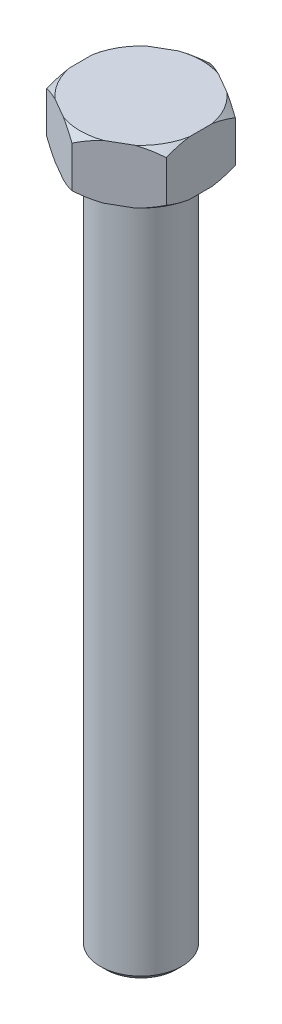
SolidWorks part; units mm, degrees
ref_plane "Front Plane" through (0, 0, 0) normal (0, 0, 1) x (1, 0, 0)
ref_plane "Top Plane" through (0, 0, 0) normal (0, 1, 0) x (1, 0, 0)
ref_plane "Right Plane" through (0, 0, 0) normal (1, 0, 0) x (0, 0, -1)
sketch "Sketch1" plane through (0, 0, 0) normal (0, 1, 0) x (1, 0, 0)
  line L1 (-11, 6.3509) -> (-11, -6.3509)
  line L2 (-11, -6.3509) -> (0, -12.7017)
  line L3 (0, -12.7017) -> (11, -6.3509)
  line L4 (11, -6.3509) -> (11, 6.3509)
  line L5 (11, 6.3509) -> (0, 12.7017)
  line L6 (0, 12.7017) -> (-11, 6.3509)
  circle A0 centre (0, 0) radius 11 construction
  point P1 (0, 0)
  point P10 (0, 0)
  dimension "D1" = 22
extrude "Boss-Extrude1" add sketch "Sketch1" along normal blind 10 contours L1 L2 L3 L4 L5 L6
sketch "Sketch2" plane through (0, 0, 0) normal (0, -1, 0) x (1, 0, 0)
  circle A0 centre (0, 0) radius 7.5
  dimension "D1" = 15
extrude "Boss-Extrude2" add sketch "Sketch2" along normal blind 126
cosmetic thread "Cosmetic Thread1"
chamfer "Chamfer1" distance 1 angle 45 1 edges at (0, -126, -7.5)
sketch "Sketch4" plane through (0, 0, 0) normal (1, 0, 0) x (0, 0, -1)
  line L0 (0, 0) -> (0, 22.1948) construction
  line L1 (12.7017, 10) -> (12.7017, 8.8)
  line L2 (12.7017, 10) -> (12.7017, 0) construction
  line L3 (12.7017, 8.8) -> (11.2017, 10)
  line L4 (12.7017, 10) -> (6.3509, 10) construction
  line L5 (11.2017, 10) -> (12.7017, 10)
  line L6 (12.7017, 1.2) -> (12.7017, 0)
  line L7 (12.7017, 0) -> (11.2017, 0)
  line L8 (12.7017, 0) -> (6.3509, 0) construction
  line L9 (11.2017, 0) -> (12.7017, 1.2)
  dimension "D1" = 1.5
  dimension "D2" = 1.2
revolve "Cut-Revolve2" cut sketch "Sketch4" angle 360 about L0
